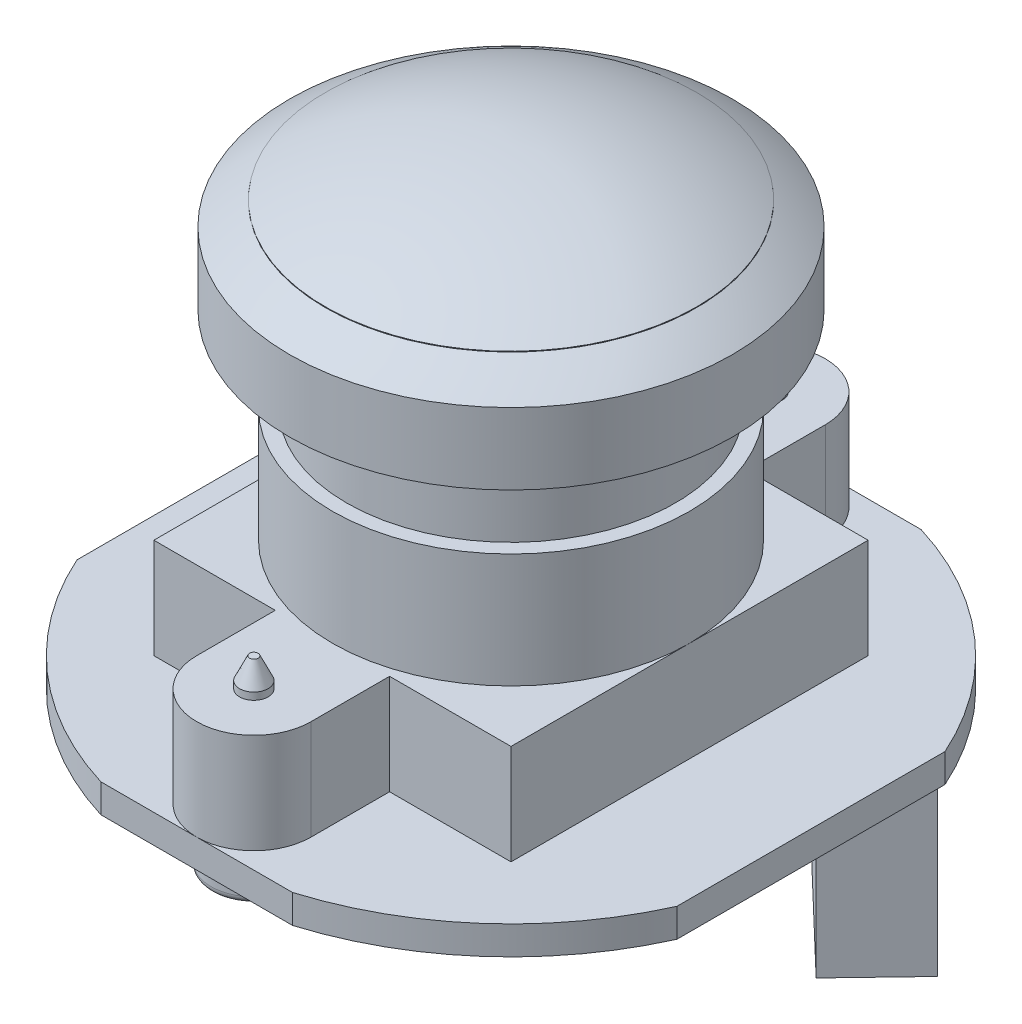
SolidWorks part; units mm, degrees
ref_plane "Front" through (0, 0, 0) normal (0, 0, 1) x (1, 0, 0)
ref_plane "Top" through (0, 0, 0) normal (0, 1, 0) x (1, 0, 0)
ref_plane "Right" through (0, 0, 0) normal (1, 0, 0) x (0, 0, -1)
sketch "Sketch1" plane through (0, 0, 0) normal (0, 1, 0) x (1, 0, 0)
  line L0 (-3.3541, 11) -> (3.3541, 11)
  line L1 (-3.3541, -11) -> (3.3541, -11)
  line L2 (-10.5, 4.6904) -> (-10.5, -4.6904)
  line L3 (10.5, -4.6904) -> (10.5, 4.6904)
  arc A0 (-3.3541, 11) -> (-10.5, 4.6904) centre (0, 0) ccw
  arc A1 (3.3541, -11) -> (10.5, -4.6904) centre (0, 0) ccw
  arc A2 (-10.5, -4.6904) -> (-3.3541, -11) centre (0, 0) ccw
  arc A3 (10.5, 4.6904) -> (3.3541, 11) centre (0, 0) ccw
  dimension "D1" = 23
  dimension "D2" = 22
  dimension "D3" = 21
extrude "Boss-Extrude1" add sketch "Sketch1" along normal blind 1
sketch "Sketch2" plane through (0, 0, 0) normal (0, -1, 0) x (1, 0, 0)
  line L0 (8.1097, -2.5702) -> (10.1842, -4.7374)
  line L1 (10.1842, -4.7374) -> (4.4051, -10.2693)
  line L2 (4.4051, -10.2693) -> (2.3306, -8.1021)
  line L3 (2.3306, -8.1021) -> (8.1097, -2.5702)
  dimension "D1" = 3
  dimension "D2" = 8
extrude "Boss-Extrude2" add sketch "Sketch2" along normal blind 6
sketch "Sketch4" plane through (0, 0, 0) normal (0, -1, 0) x (1, 0, 0)
  line L0 (0, -9) -> (0, 9) construction
  line L2 (8.1097, -2.5702) -> (2.3306, -8.1021) construction
  line L3 (-1.3644, 1.3186) -> (5.1356, 1.3186)
  line L4 (-1.3644, 1.3186) -> (-1.3644, -5.1814)
  line L5 (-1.3644, -5.1814) -> (5.1356, -5.1814)
  line L6 (5.1356, 1.3186) -> (5.1356, -5.1814)
  line L7 (8.1097, -2.5702) -> (2.3306, -8.1021) construction
  line L8 (-6.7897, 7.6336) -> (-2.5646, 4.7811)
  line L9 (-2.5646, 4.7811) -> (-5.2333, 0.8282)
  line L10 (-5.2333, 0.8282) -> (-9.4584, 3.6807)
  line L11 (-9.4584, 3.6807) -> (-6.7897, 7.6336)
  line L12 (7.5379, 3.877) -> (8.5222, 3.877) construction
  line L13 (-7.97, -1.8845) -> (-4.057, -1.8845)
  line L14 (-7.97, -1.8845) -> (-7.97, -7.9821)
  line L15 (-7.97, -7.9821) -> (-4.057, -7.9821)
  line L16 (-4.057, -1.8845) -> (-4.057, -7.9821)
  line L17 (7.5379, 4.2611) -> (8.5222, 4.2611)
  line L18 (7.5379, 3.4929) -> (8.5222, 3.4929)
  line L19 (7.5499, 2.8927) -> (8.5342, 2.8927) construction
  line L20 (7.5499, 3.2768) -> (8.5342, 3.2768)
  line L21 (7.5499, 2.5086) -> (8.5342, 2.5086)
  line L22 (7.3939, -0.156) -> (8.3782, -0.156) construction
  line L23 (7.3939, 0.2281) -> (8.3782, 0.2281)
  line L24 (7.3939, -0.5401) -> (8.3782, -0.5401)
  line L25 (7.4059, -1.1403) -> (8.3902, -1.1403) construction
  line L26 (7.4059, -0.7562) -> (8.3902, -0.7562)
  line L27 (7.4059, -1.5244) -> (8.3902, -1.5244)
  circle A0 centre (0, -9) radius 1.5
  circle A1 centre (0, 9) radius 1.5
  arc A2 (7.5379, 4.2611) -> (7.5379, 3.4929) centre (7.5379, 3.877) ccw
  arc A3 (8.5222, 3.4929) -> (8.5222, 4.2611) centre (8.5222, 3.877) ccw
  arc A4 (7.5499, 3.2768) -> (7.5499, 2.5086) centre (7.5499, 2.8927) ccw
  arc A5 (8.5342, 2.5086) -> (8.5342, 3.2768) centre (8.5342, 2.8927) ccw
  arc A6 (7.3939, 0.2281) -> (7.3939, -0.5401) centre (7.3939, -0.156) ccw
  arc A7 (8.3782, -0.5401) -> (8.3782, 0.2281) centre (8.3782, -0.156) ccw
  arc A8 (7.4059, -0.7562) -> (7.4059, -1.5244) centre (7.4059, -1.1403) ccw
  arc A9 (8.3902, -1.5244) -> (8.3902, -0.7562) centre (8.3902, -1.1403) ccw
  point P5 (0, 0)
  point P23 (8.0301, 3.877)
  point P30 (8.0421, 2.8927)
  point P37 (7.886, -0.156)
  point P44 (7.898, -1.1403)
  point P49 (-4.057, -1.8845)
  point P50 (-4.4651, 1.3083)
  point P51 (-5.7855, -0.7562)
  point P52 (0, 0)
  point P53 (5.0766, -5.0636)
  dimension "D1" = 18
  dimension "D2" = 3
  dimension "D3" = 6.5
extrude "Boss-Extrude6" add sketch "Sketch4" along normal blind 1
fillet "Fillet1" radius 0.25 2 edges at (0, -1, -10.5) (0, -1, 7.5)
sketch "Sketch5" plane through (0, 1, 0) normal (0, 1, 0) x (1, 0, 0)
  line L0 (-2, -6.25) -> (-2, -9)
  line L5 (-6.25, -6.25) -> (-2, -6.25)
  line L6 (-6.25, -6.25) -> (-6.25, 6.25)
  line L7 (-6.25, 6.25) -> (-2, 6.25)
  line L8 (6.25, -6.25) -> (6.25, 6.25)
  line L9 (-6.25, -6.25) -> (6.25, 6.25) construction
  line L10 (-6.25, 6.25) -> (6.25, -6.25) construction
  line L11 (2, -6.25) -> (2, -9)
  line L12 (0, 0) -> (0, -6.25) construction
  line L13 (0, 0) -> (6.25, 0) construction
  line L14 (-2, 6.25) -> (-2, 9)
  line L15 (2, 6.25) -> (2, 9)
  line L16 (2, 6.25) -> (6.25, 6.25)
  line L17 (2, -6.25) -> (6.25, -6.25)
  arc A0 (-2, -9) -> (2, -9) centre (0, -9) ccw
  arc A1 (-2, 9) -> (2, 9) centre (0, 9) cw
  point P0 (0, 0)
  dimension "D1" = 12.5
  dimension "D2" = 2
  dimension "D3" = 18
  dimension "D4" = 12.5
extrude "Boss-Extrude7" add sketch "Sketch5" along normal blind 3.5
sketch "Sketch6" plane through (0, 4.5, 0) normal (0, 1, 0) x (1, 0, 0)
  circle A0 centre (0, 0) radius 6.25
  dimension "D1" = 12.5
extrude "Boss-Extrude8" add sketch "Sketch6" along normal blind 4
sketch "Sketch7" plane through (0, 4.5, 0) normal (0, 1, 0) x (1, 0, 0)
  arc A0 (0, -11) -> (2, -9) centre (0, -9) ccw construction
  arc A1 (2, 9) -> (-2, 9) centre (0, 9) ccw construction
  arc A2 (0, -11) -> (2, -9) centre (0, -9) ccw construction
  arc A3 (2, 9) -> (-2, 9) centre (0, 9) ccw construction
  circle A4 centre (0, 9) radius 0.5
  circle A5 centre (0, -9) radius 0.5
  dimension "D1" = 1
extrude "Boss-Extrude9" add sketch "Sketch7" along normal blind 1
chamfer "Chamfer1" distance 0.75 angle 25 2 edges at (0, 5.5, 9.5) (0, 5.5, -8.5)
sketch "Sketch8" plane through (0, 0, 0) normal (0, 0, 1) x (1, 0, 0)
  line L1 (6.25, 4.5) -> (-6.25, 4.5) construction
  line L2 (6.25, 4.5) -> (-6.25, 4.5) construction
  line L3 (0, 4.5) -> (0, 16.5)
  line L4 (0.7353, 16.5) -> (7.7811, 16.5) construction
  line L5 (7.75, 14) -> (7.75, 11.5)
  line L6 (7.75, 11.5) -> (5.75, 11.5)
  line L7 (5.75, 11.5) -> (5.75, 4.5)
  line L8 (5.75, 4.5) -> (0, 4.5)
  line L9 (0, 16.5) -> (0, 16.525)
  line L10 (6.5, 14.7979) -> (6.5, 14.8229)
  line L11 (0, 16.525) -> (-0.2989, 16.525) construction
  arc A0 (0, 16.5) -> (7.75, 14) centre (0, 3.2375) cw construction
  arc A1 (0, 16.525) -> (6.5, 14.8229) centre (0, 3.2625) cw
  arc A2 (6.5, 14.7979) -> (7.75, 14) centre (0, 3.2375) cw
  dimension "D1" = 12
  dimension "D2" = 7.75
  dimension "D3" = 9.5
  dimension "D4" = 2.5
  dimension "D5" = 5.75
  dimension "D6" = 0.025
  dimension "D7" = 6.5
revolve "Revolve1" add sketch "Sketch8" angle 360 about L3
